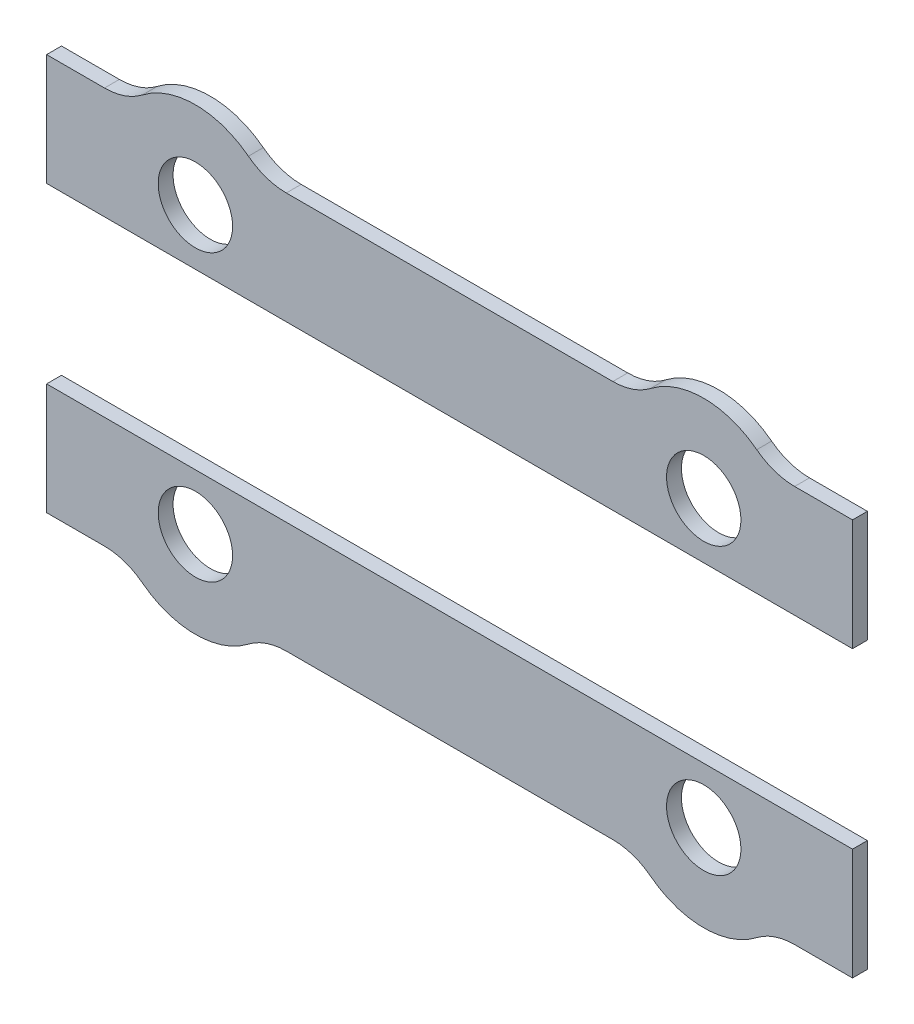
SolidWorks part; units mm, degrees
ref_plane "Alzado" through (0, 0, 0) normal (0, 0, 1) x (1, 0, 0)
ref_plane "Planta" through (0, 0, 0) normal (0, 1, 0) x (1, 0, 0)
ref_plane "Vista lateral" through (0, 0, 0) normal (1, 0, 0) x (0, 0, -1)
sketch "Sketch1" plane through (0, 14.6, 0) normal (0, 0, 1) x (1, 0, 0)
  line L0 (0, -10.1) -> (0, -14.6)
  line L1 (0, -14.6) -> (2.3343, -14.6)
  line L2 (9.6657, -14.6) -> (22.8343, -14.6)
  line L4 (0, -10.1) -> (32.5, -10.1)
  line L6 (16.25, -10.1) -> (16.25, -14.6)
  line L7 (0, -10.1) -> (0, -3.1)
  line L8 (0, -6.6) -> (32.5, -6.6)
  line L9 (16.25, -3.1) -> (16.25, -10.1)
  line L10 (16.25, -3.1) -> (16.25, 1.4)
  line L11 (9.6657, 1.4) -> (22.8343, 1.4)
  line L12 (0, -3.1) -> (32.5, -3.1)
  line L13 (0, 1.4) -> (2.3343, 1.4)
  line L14 (0, -3.1) -> (0, 1.4)
  line L15 (32.5, -3.1) -> (32.5, 1.4)
  line L16 (32.5, 1.4) -> (30.1657, 1.4)
  line L17 (32.5, -10.1) -> (32.5, -3.1)
  line L18 (32.5, -14.6) -> (30.1657, -14.6)
  line L19 (32.5, -10.1) -> (32.5, -14.6)
  arc A0 (9.6657, -14.6) -> (8.1383, -15.1208) centre (9.6657, -17.1) ccw
  arc A1 (8.1383, -15.1208) -> (8.8588, -14.7338) centre (9.6657, -17.1) cw
  arc A2 (8.1383, -15.1208) -> (3.8617, -15.1208) centre (6, -12.35) cw
  arc A3 (3.8617, -15.1208) -> (4.7368, -15.6141) centre (6, -12.35) ccw
  arc A4 (4.7368, -15.6141) -> (3.8617, -15.1208) centre (6, -12.35) cw
  arc A5 (2.3343, -14.6) -> (2.4053, -14.601) centre (2.3343, -17.1) cw
  circle A7 centre (6, -12.35) radius 1.5
  arc A8 (2.4053, -14.601) -> (3.8617, -15.1208) centre (2.3343, -17.1) cw
  arc A9 (2.4053, 1.401) -> (3.8617, 1.9208) centre (2.3343, 3.9) ccw
  circle A10 centre (6, -0.85) radius 1.5
  arc A11 (2.3343, 1.4) -> (2.4053, 1.401) centre (2.3343, 3.9) ccw
  arc A12 (4.7368, 2.4141) -> (3.8617, 1.9208) centre (6, -0.85) ccw
  arc A13 (3.8617, 1.9208) -> (4.7368, 2.4141) centre (6, -0.85) cw
  arc A14 (8.1383, 1.9208) -> (3.8617, 1.9208) centre (6, -0.85) ccw
  arc A15 (8.1383, 1.9208) -> (8.8588, 1.5338) centre (9.6657, 3.9) ccw
  arc A16 (9.6657, 1.4) -> (8.1383, 1.9208) centre (9.6657, 3.9) cw
  arc A17 (22.8343, 1.4) -> (24.3617, 1.9208) centre (22.8343, 3.9) ccw
  arc A18 (24.3617, 1.9208) -> (23.6412, 1.5338) centre (22.8343, 3.9) cw
  arc A19 (24.3617, 1.9208) -> (28.6383, 1.9208) centre (26.5, -0.85) cw
  arc A20 (28.6383, 1.9208) -> (27.7632, 2.4141) centre (26.5, -0.85) ccw
  arc A21 (27.7632, 2.4141) -> (28.6383, 1.9208) centre (26.5, -0.85) cw
  arc A22 (30.1657, 1.4) -> (30.0947, 1.401) centre (30.1657, 3.9) cw
  circle A23 centre (26.5, -0.85) radius 1.5
  arc A24 (30.0947, 1.401) -> (28.6383, 1.9208) centre (30.1657, 3.9) cw
  arc A25 (30.0947, -14.601) -> (28.6383, -15.1208) centre (30.1657, -17.1) ccw
  circle A26 centre (26.5, -12.35) radius 1.5
  arc A27 (30.1657, -14.6) -> (30.0947, -14.601) centre (30.1657, -17.1) ccw
  arc A28 (27.7632, -15.6141) -> (28.6383, -15.1208) centre (26.5, -12.35) ccw
  arc A29 (28.6383, -15.1208) -> (27.7632, -15.6141) centre (26.5, -12.35) cw
  arc A30 (24.3617, -15.1208) -> (28.6383, -15.1208) centre (26.5, -12.35) ccw
  arc A31 (24.3617, -15.1208) -> (23.6412, -14.7338) centre (22.8343, -17.1) ccw
  arc A32 (22.8343, -14.6) -> (24.3617, -15.1208) centre (22.8343, -17.1) cw
  point P68 (16.25, -6.6)
  dimension "D1" = 3
  dimension "D5" = 3.5
  dimension "D6" = 2.5
  dimension "D9" = 2.5
  dimension "D10" = 6.5843
  dimension "D4" = 7.3314
  dimension "D2" = 4.5
  dimension "D3" = 3.5
  dimension "D8" = 2.3343
  dimension "D11" = 4.5
  dimension "D12" = 5.75
extrude "Boss-Extrude1" add sketch "Sketch1" along normal blind 0.6 contours L11 A16 A15 A14 A12 A9 A11 L13 L14 L12 L10 A10 | A5 A8 A2 A0 L2 L6 L4 L0 L1 A7 | A22 A24 A19 A17 L11 L10 L12 L15 L16 A23 | L2 A32 A31 A30 A28 A25 A27 L18 L19 L4 L6 A26
